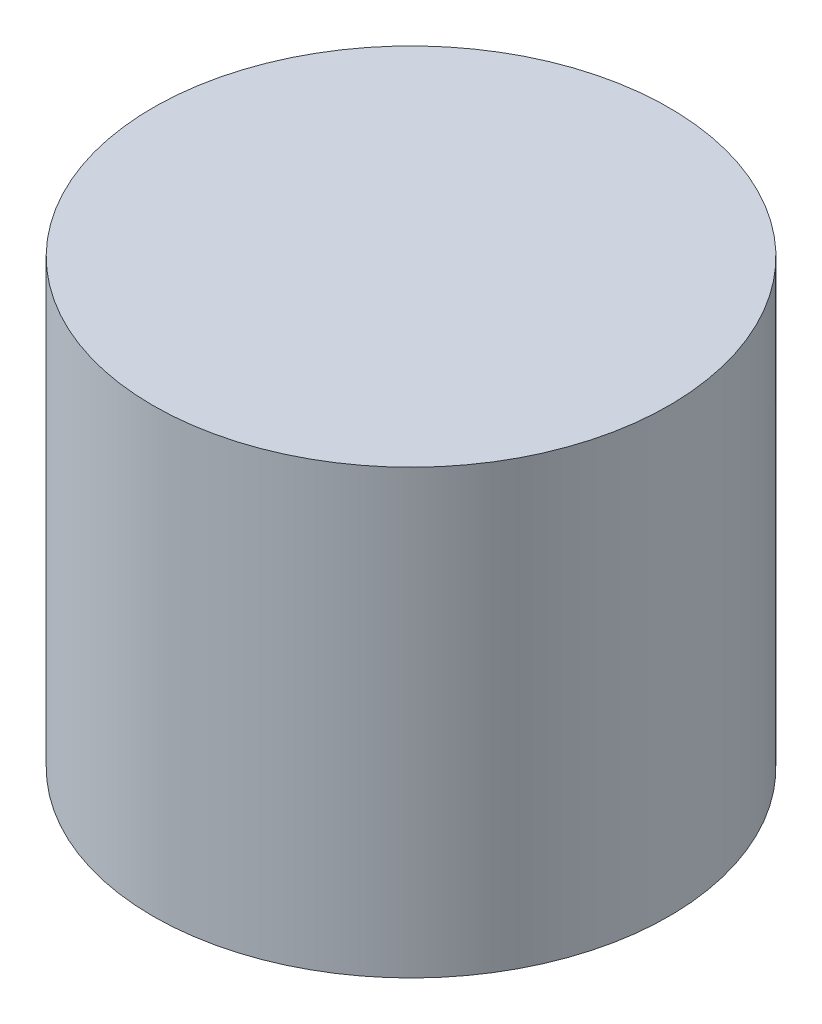
SolidWorks part; units mm, degrees
ref_plane "Front Plane" through (0, 0, 0) normal (0, 0, 1) x (1, 0, 0)
ref_plane "Top Plane" through (0, 0, 0) normal (0, 1, 0) x (1, 0, 0)
ref_plane "Right Plane" through (0, 0, 0) normal (1, 0, 0) x (0, 0, -1)
sketch "Sketch1" plane through (0, 0, 0) normal (0, 1, 0) x (1, 0, 0)
  circle A0 centre (0, 0) radius 7
  dimension "D1" = 14
extrude "Boss-Extrude1" add sketch "Sketch1" along normal blind 12
sketch "Sketch2" plane through (0, 0, 0) normal (0, -1, 0) x (1, 0, 0)
  line L0 (-2.75, -1) -> (2.75, -1)
  circle A1 centre (0, 0) radius 2.9262 construction
  arc A2 (-2.75, -1) -> (2.75, -1) centre (0, 0) cw
  point P2 (0, -1)
  dimension "D2" = 1
  dimension "D1" = 5.5
extrude "Cut-Extrude1" cut sketch "Sketch2" against normal blind 7
